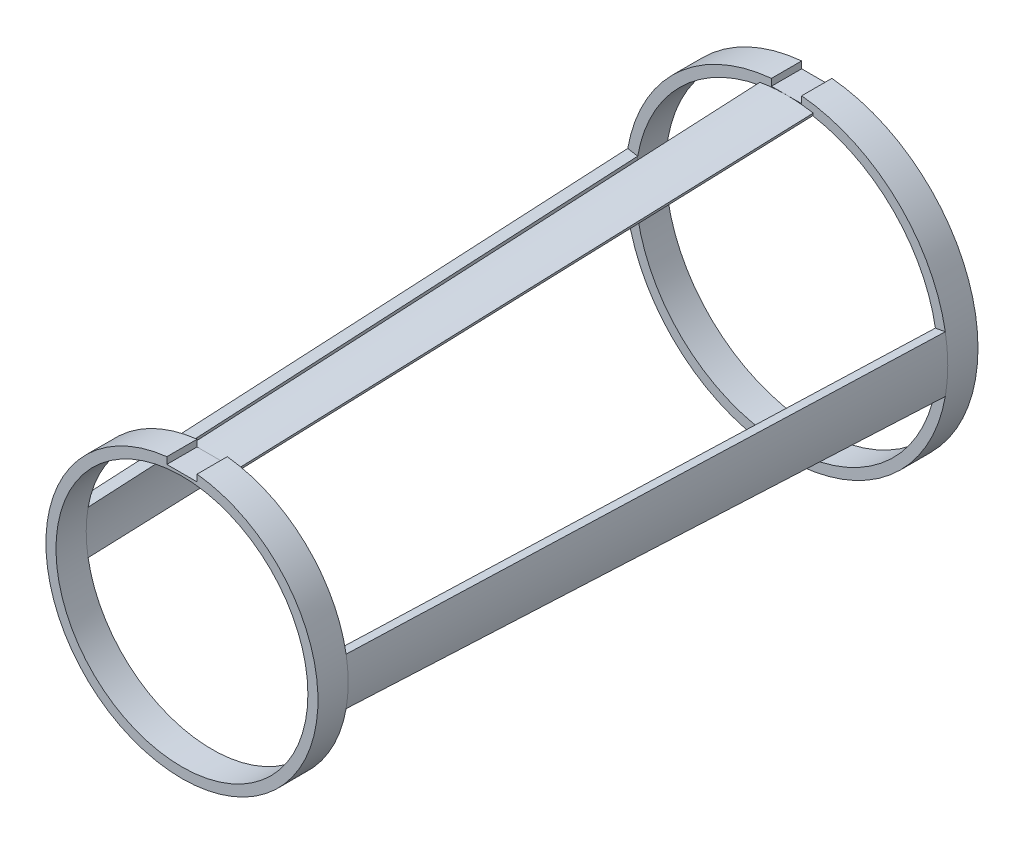
SolidWorks part; units mm, degrees
material "Thornel Mat VMA"
ref_plane "Front Plane" through (0, 0, 0) normal (0, 0, 1) x (1, 0, 0)
ref_plane "Top Plane" through (0, 0, 0) normal (0, 1, 0) x (1, 0, 0)
ref_plane "Right Plane" through (0, 0, 0) normal (1, 0, 0) x (0, 0, -1)
sketch "Sketch1" plane through (0, 0, 0) normal (0, 0, 1) x (1, 0, 0)
  circle A0 centre (0, 0) radius 38.1
  circle A1 centre (0, 0) radius 40.64
  dimension "D1" = 76.2
  dimension "D2" = 2.54
extrude "Boss-Extrude1" add sketch "Sketch1" along normal mid plane 7.62
sketch "Sketch2" plane through (0, 0, 0) normal (0, 0, 1) x (1, 0, 0)
  line L1 (-3.81, 38.735) -> (3.81, 38.735)
  line L2 (-3.81, 38.735) -> (-3.81, 42.545)
  line L3 (-3.81, 42.545) -> (3.81, 42.545)
  line L4 (3.81, 38.735) -> (3.81, 42.545)
  line L5 (-3.81, 38.735) -> (3.81, 42.545) construction
  line L6 (-3.81, 42.545) -> (3.81, 38.735) construction
  circle A0 centre (0, 0) radius 40.64 construction
  point P0 (0, 40.64)
  point P7 (0, 0)
  dimension "D1" = 3.81
  dimension "D2" = 7.62
extrude "Cut-Extrude1" cut sketch "Sketch2" against normal up to next and the other way up to next
ref_plane "Plane1" through (0, 0, 152.4) normal (0, 0, 1) x (1, 0, 0)
sketch "Sketch3" plane through (0, 0, 152.4) normal (0, 0, 1) x (1, 0, 0)
  circle A0 centre (0, 0) radius 31.75
  circle A1 centre (0, 0) radius 34.29
  dimension "D1" = 63.5
  dimension "D2" = 2.54
extrude "Boss-Extrude2" add sketch "Sketch3" along normal mid plane 7.62
sketch "Sketch5" plane through (0, 0, 0) normal (0, 1, 0) x (1, 0, 0)
  line L0 (-40.64, -3.81) -> (-34.29, -148.59)
  line L1 (40.64, -3.81) -> (34.29, -148.59)
  line L2 (38.1, -3.81) -> (31.75, -148.59)
  line L3 (40.64, -3.81) -> (38.1, -3.81)
  line L4 (34.29, -148.59) -> (31.75, -148.59)
  line L5 (0, 17.1543) -> (0, -178.2895) construction
  line L6 (-34.29, -148.59) -> (-31.75, -148.59)
  line L7 (-40.64, -3.81) -> (-38.1, -3.81)
  line L8 (-38.1, -3.81) -> (-31.75, -148.59)
revolve "Revolve1" add sketch "Sketch5" angle 10 about L5 other way angle 10
sketch "Sketch6" plane through (0, 0, 156.21) normal (0, 0, 1) x (1, 0, 0)
  line L1 (-3.81, 32.385) -> (3.81, 32.385)
  line L2 (-3.81, 32.385) -> (-3.81, 36.195)
  line L3 (-3.81, 36.195) -> (3.81, 36.195)
  line L4 (3.81, 32.385) -> (3.81, 36.195)
  line L5 (-3.81, 32.385) -> (3.81, 36.195) construction
  line L6 (-3.81, 36.195) -> (3.81, 32.385) construction
  circle A0 centre (0, 0) radius 34.29 construction
  point P0 (0, 34.29)
  point P7 (0, 0)
  point P9 (0, 0)
  dimension "D1" = 3.81
  dimension "D2" = 7.62
extrude "Cut-Extrude2" cut sketch "Sketch6" against normal up to next
sketch "Sketch11" plane through (0, 0, 0) normal (1, 0, 0) x (0, 0, -1)
  line L0 (-148.59, 32.385) -> (-3.81, 38.735)
  line L1 (-148.59, 31.75) -> (-3.81, 38.1)
  line L2 (-148.59, 32.385) -> (-148.59, 31.75)
  line L3 (-3.81, 38.735) -> (-3.81, 38.1)
  line L4 (0, 0) -> (-148.59, 0) construction
  line L5 (-148.59, 5.9544) -> (-148.59, -5.9544) construction
revolve "Revolve2" add sketch "Sketch11" angle 10 about L4 other way angle 10
